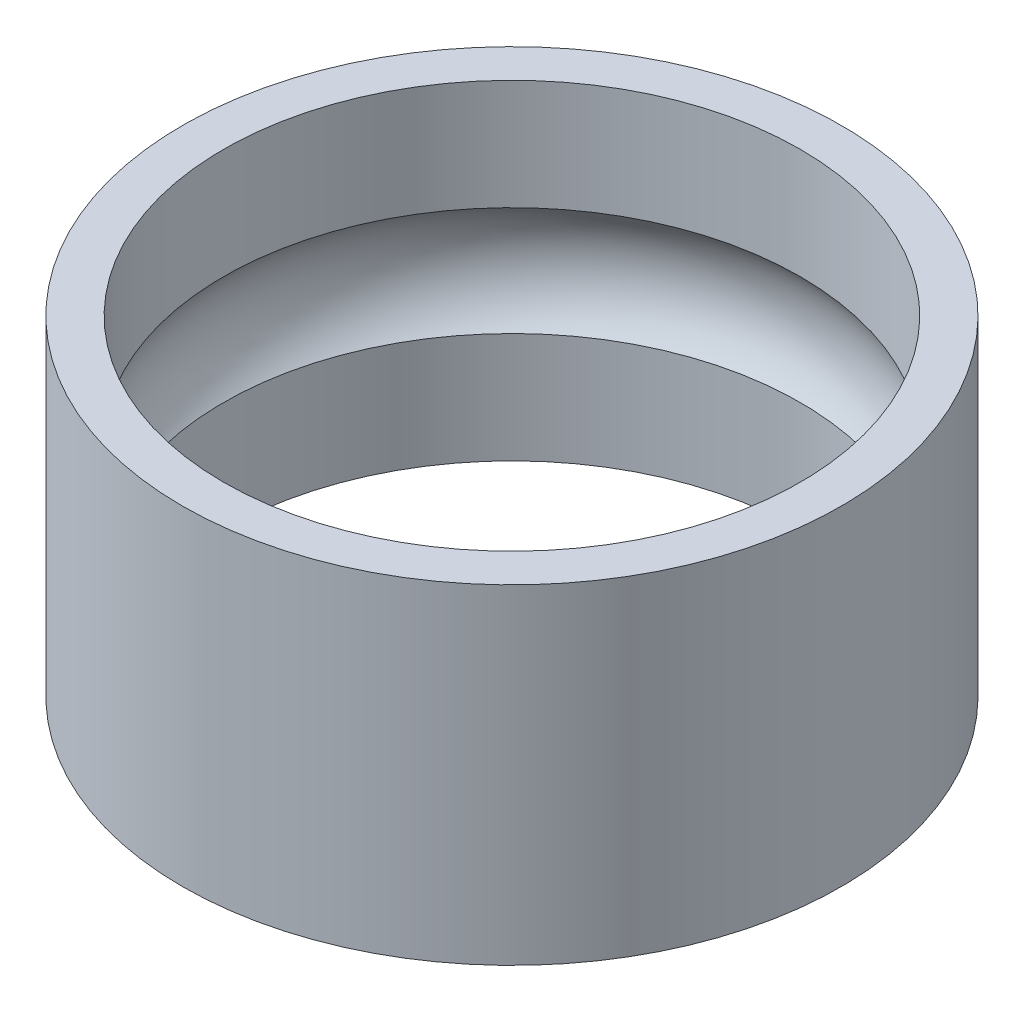
SolidWorks part; units mm, degrees
material "Chrome Stainless Steel"
ref_plane "Front Plane" through (0, 0, 0) normal (0, 0, 1) x (1, 0, 0)
ref_plane "Top Plane" through (0, 0, 0) normal (0, 1, 0) x (1, 0, 0)
ref_plane "Right Plane" through (0, 0, 0) normal (1, 0, 0) x (0, 0, -1)
sketch "DiaProfileS" plane through (0, 0, 0) normal (0, 1, 0) x (1, 0, 0)
  circle A0 centre (0, 0) radius 3.5
  circle A1 centre (0, 0) radius 4
  dimension "InnerDia" = 7
  dimension "Thickness" = 0.5
extrude "DiaProfile" add sketch "DiaProfileS" along normal mid plane 4
sketch "BearingPathProfileS" plane through (0, 0, 0) normal (0, 0, 1) x (1, 0, 0)
  line L1 (0, 0) -> (2.75, 0) construction
  circle A0 centre (2.75, 0) radius 1
  point P7 (3.5, 2)
  dimension "BallDia" = 2
  dimension "YDim" = 0.75
  dimension "RefRadius" = 2.75
revolve "BearingPathProfile" cut sketch "BearingPathProfileS" angle 360 about axis through (0, 2, 0) along (0, -1, 0)
